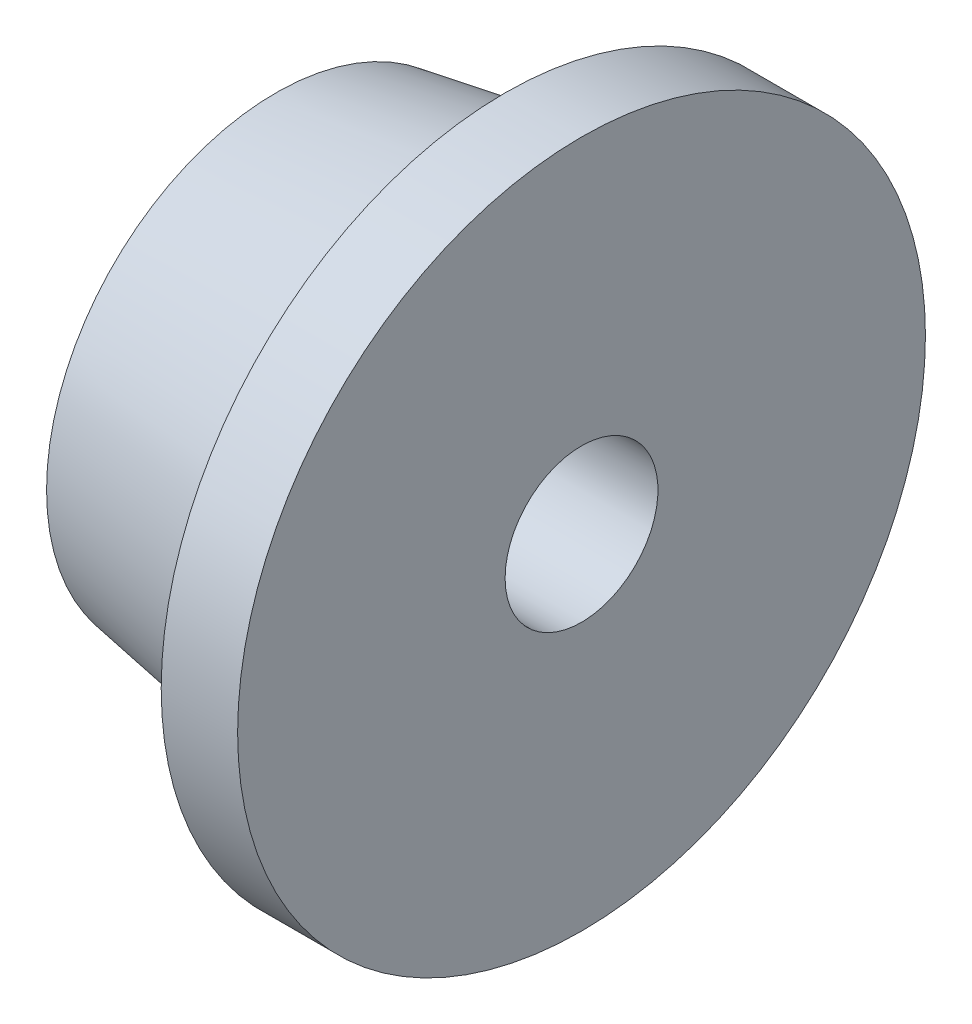
SolidWorks part; units mm, degrees
ref_plane "Front Plane" through (0, 0, 0) normal (0, 0, 1) x (1, 0, 0)
ref_plane "Top Plane" through (0, 0, 0) normal (0, 1, 0) x (1, 0, 0)
ref_plane "Right Plane" through (0, 0, 0) normal (1, 0, 0) x (0, 0, -1)
sketch "Sketch1" plane through (0, 0, 0) normal (0, 0, 1) x (1, 0, 0)
  line L0 (-11.4712, 0) -> (19.7688, 0) construction
  line L1 (0.9275, 4.5) -> (1.9275, 4.5)
  line L2 (1.9275, 4.5) -> (1.9275, 1)
  line L3 (-2.0725, 1) -> (-2.0725, 3)
  line L4 (0.9275, 4.5) -> (0.9275, 3.5)
  line L7 (-2.0725, 1) -> (1.9275, 1)
  line L8 (-2.0725, 3) -> (0.9275, 3.5)
  dimension "D1" = 9
  dimension "D2" = 1
  dimension "D3" = 6
  dimension "D4" = 2
  dimension "D5" = 4
  dimension "D6" = 7
revolve "Revolve1" add sketch "Sketch1" angle 360 about L0
